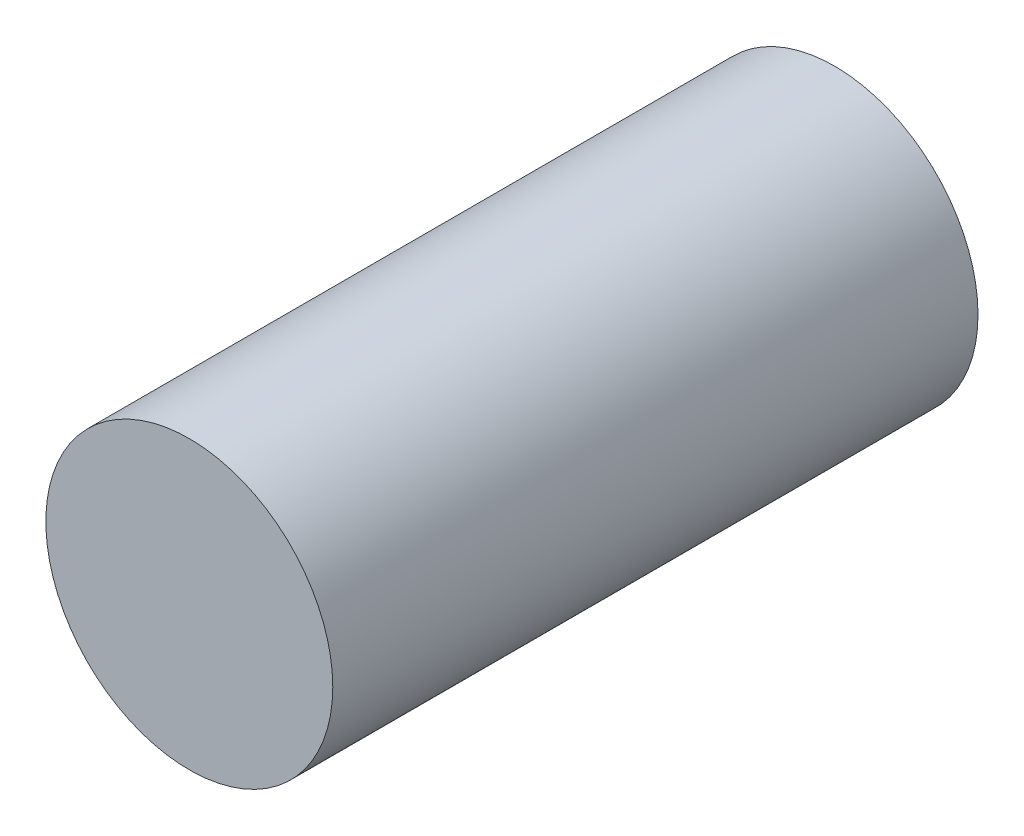
SolidWorks part; units mm, degrees
material "Nichel"
ref_plane "Piano frontale" through (0, 0, 0) normal (0, 0, 1) x (1, 0, 0)
ref_plane "Piano superiore" through (0, 0, 0) normal (0, 1, 0) x (1, 0, 0)
ref_plane "Piano destro" through (0, 0, 0) normal (1, 0, 0) x (0, 0, -1)
sketch "Schizzo1" plane through (0, 0, 0) normal (0, 0, 1) x (1, 0, 0)
  circle A0 centre (0, 0) radius 58.7
extrude "Estrusione-Estrusione1" add sketch "Schizzo1" along normal blind 5
sketch "Schizzo2" plane through (0, 0, 5) normal (0, 0, 1) x (1, 0, 0)
  circle A0 centre (0, 0) radius 58.7
  circle A1 centre (0, 0) radius 48.7
  circle A2 centre (0, 0) radius 58.7 construction
  dimension "D1" = 10
extrude "Estrusione-Estrusione2" add sketch "Schizzo2" along normal blind 254
sketch "Schizzo3" plane through (0, 0, 259) normal (0, 0, 1) x (1, 0, 0)
  circle A0 centre (0, 0) radius 58.7
extrude "Estrusione-Estrusione3" add sketch "Schizzo3" along normal blind 5
